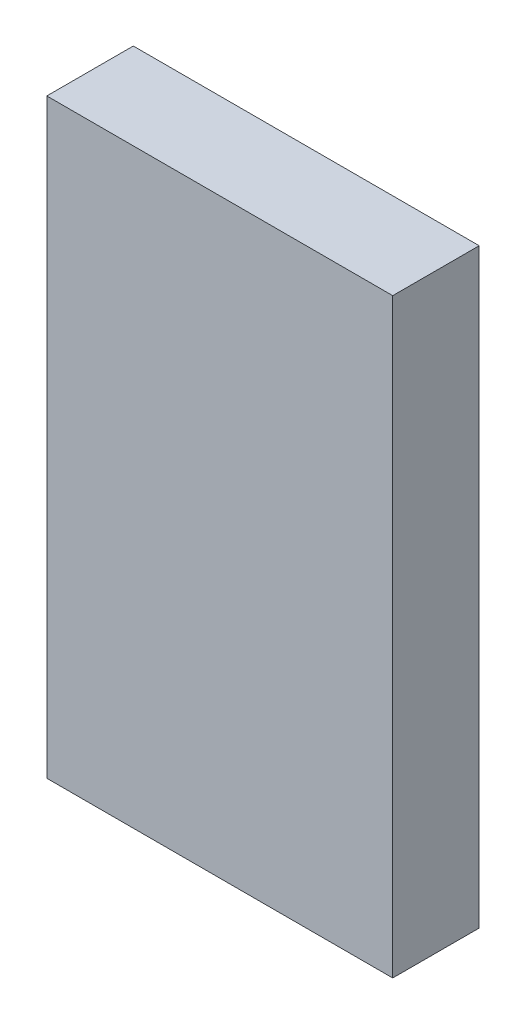
SolidWorks part; units mm, degrees
ref_plane "Front Plane" through (0, 0, 0) normal (0, 0, 1) x (1, 0, 0)
ref_plane "Top Plane" through (0, 0, 0) normal (0, 1, 0) x (1, 0, 0)
ref_plane "Right Plane" through (0, 0, 0) normal (1, 0, 0) x (0, 0, -1)
sketch "Sketch1" plane through (0, 0, 0) normal (0, 0, 1) x (1, 0, 0)
  line L1 (0, 0) -> (120, 0)
  line L2 (0, 0) -> (0, -205)
  line L3 (0, -205) -> (120, -205)
  line L4 (120, 0) -> (120, -205)
  dimension "D1" = 120
  dimension "D2" = 205
extrude "Boss-Extrude1" add sketch "Sketch1" along normal blind 30
